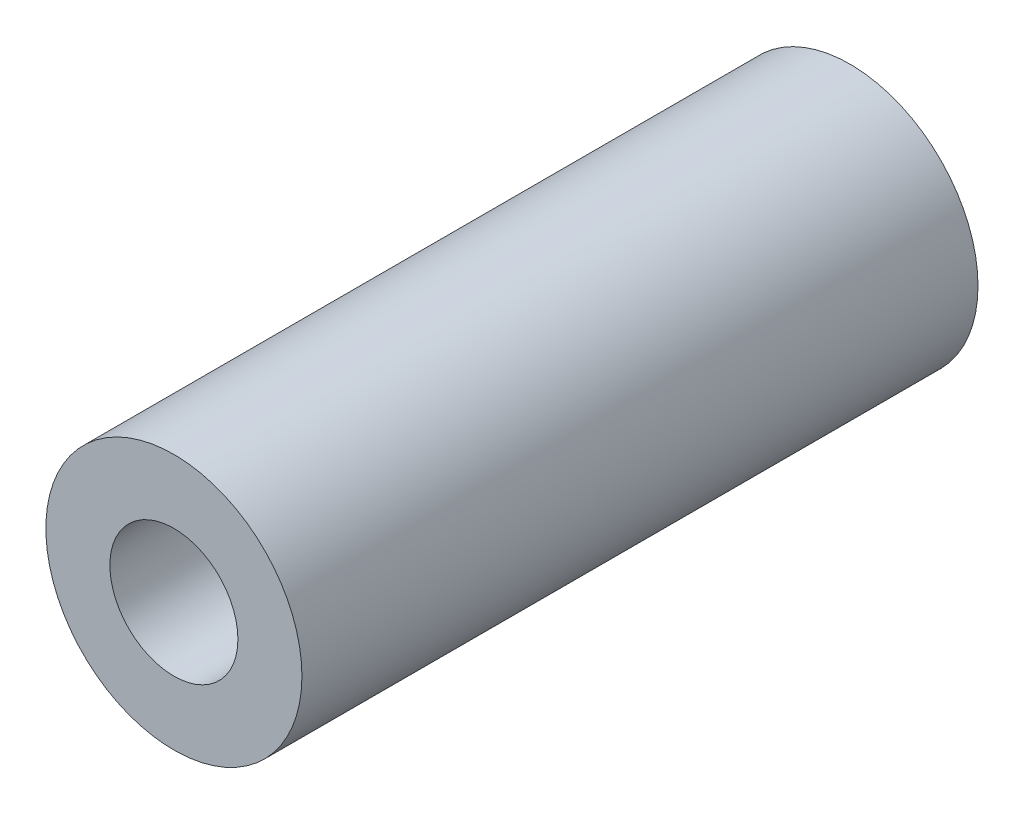
SolidWorks part; units mm, degrees
ref_plane "Front Plane" through (0, 0, 0) normal (0, 0, 1) x (1, 0, 0)
ref_plane "Top Plane" through (0, 0, 0) normal (0, 1, 0) x (1, 0, 0)
ref_plane "Right Plane" through (0, 0, 0) normal (1, 0, 0) x (0, 0, -1)
sketch "Sketch1" plane through (0, 0, 0) normal (0, 0, 1) x (1, 0, 0)
  circle A0 centre (0, 0) radius 5
  dimension "D1" = 10
extrude "Boss-Extrude1" add sketch "Sketch1" along normal blind 26.4
hole_wizard "Ø5.0mm Dowel Hole1" positions "Sketch2" profile "Sketch3" hole size "Ø5.0" standard "ANSI Metric" end condition up to next
sketch "Sketch2" plane through (0, 0, 26.4) normal (0, 0, 1) x (1, 0, 0)
  point P0 (0, 0)
sketch "Sketch3" plane through (0, 0, 26.4) normal (1, 0, 0) x (0, -1, 0)
  line L0 (0, 0) -> (0, 26.4)
  line L1 (0, 26.4) -> (2.5, 26.4)
  line L2 (2.5, 26.4) -> (2.5, 0)
  line L5 (2.5, 0) -> (0, 0)
  line L11 (0, -6.35) -> (0, 107.95) construction
  dimension "Thru Hole Dia." = 5
  dimension "Thru Hole Depth" = 26.4
